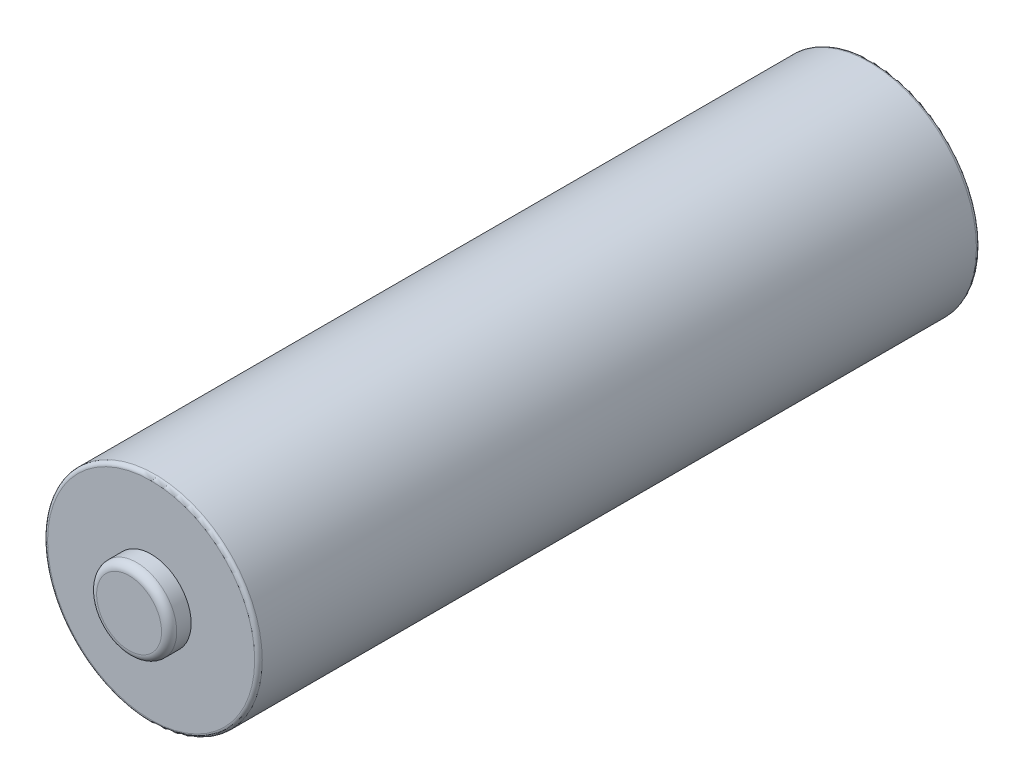
SolidWorks part; units mm, degrees
ref_plane "Front Plane" through (0, 0, 0) normal (0, 0, 1) x (1, 0, 0)
ref_plane "Top Plane" through (0, 0, 0) normal (0, 1, 0) x (1, 0, 0)
ref_plane "Right Plane" through (0, 0, 0) normal (1, 0, 0) x (0, 0, -1)
sketch "Sketch1" plane through (0, 0, 0) normal (0, 0, 1) x (1, 0, 0)
  circle A0 centre (0, 0) radius 7.065
  dimension "D1" = 14.13
extrude "Boss-Extrude1" add sketch "Sketch1" along normal blind 47.5
sketch "Sketch2" plane through (0, 0, 47.5) normal (0, 0, 1) x (1, 0, 0)
  circle A0 centre (0, 0) radius 2.635
  dimension "D1" = 5.27
extrude "Boss-Extrude2" add sketch "Sketch2" along normal blind 1.45
fillet "Fillet2" radius 0.25 2 edges at (7.065, 0, 0) (7.065, 0, 47.5)
sketch "Sketch3" plane through (0, 0, 0) normal (0, 0, -1) x (-1, 0, 0)
  circle A0 centre (0, 0) radius 4.435
  dimension "D1" = 8.87
extrude "Boss-Extrude3" add sketch "Sketch3" along normal blind 1.2
fillet "Fillet1" radius 0.5 2 edges at (2.635, 0, 48.95) (-4.435, 0, -1.2)
